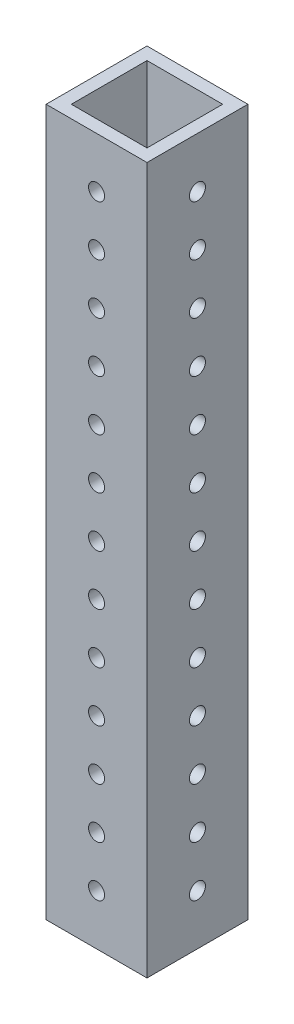
SolidWorks part; units mm, degrees
material "6061 Alloy"
ref_plane "Front Plane" through (0, 0, 0) normal (0, 0, 1) x (1, 0, 0)
ref_plane "Top Plane" through (0, 0, 0) normal (0, 1, 0) x (1, 0, 0)
ref_plane "Right Plane" through (0, 0, 0) normal (1, 0, 0) x (0, 0, -1)
sketch "Sketch1" plane through (0, 0, 0) normal (0, 1, 0) x (1, 0, 0)
  line L0 (9.525, 9.525) -> (-9.525, 9.525)
  line L1 (12.7, -12.7) -> (-12.7, -12.7)
  line L2 (12.7, -12.7) -> (12.7, 12.7)
  line L3 (12.7, 12.7) -> (-12.7, 12.7)
  line L4 (-12.7, -12.7) -> (-12.7, 12.7)
  line L5 (12.7, -12.7) -> (-12.7, 12.7) construction
  line L6 (12.7, 12.7) -> (-12.7, -12.7) construction
  line L7 (-9.525, -9.525) -> (-9.525, 9.525)
  line L8 (9.525, -9.525) -> (-9.525, -9.525)
  line L9 (9.525, -9.525) -> (9.525, 9.525)
  point P0 (0, 0)
  dimension "D1" = 25.4
  dimension "D2" = 25.4
  dimension "D3" = 3.175
extrude "Boss-Extrude1" add sketch "Sketch1" along normal blind 177.8
hole_wizard "#21 (0.159) Diameter Hole1" positions "Sketch2" profile "Sketch3" hole size "#21" standard "ANSI Inch" end condition through all
sketch "Sketch2" plane through (-12.7, 0, 0) normal (-1, 0, 0) x (0, 0, 1)
  line L0 (-12.7, 0) -> (12.7, 0) construction
  line L1 (12.7, 177.8) -> (12.7, 0) construction
  point P0 (0, 12.7)
  dimension "D1" = 12.7
  dimension "D2" = 12.7
sketch "Sketch3" plane through (-12.7, 12.7, 0) normal (0, 1, 0) x (0, 0, 1)
  line L0 (0, 0) -> (0, 25.4)
  line L1 (0, 25.4) -> (2.0193, 25.4)
  line L2 (2.0193, 25.4) -> (2.0193, 0)
  line L5 (2.0193, 0) -> (0, 0)
  line L11 (0, -6.35) -> (0, 107.95) construction
  dimension "Thru Hole Dia." = 4.0386
  dimension "Thru Hole Depth" = 25.4
pattern_linear "LPattern1" count 13 spacing 12.7 along (0, 1, 0) of "#21 (0.159) Diameter Hole1"
hole_wizard "#21 (0.159) Diameter Hole2" positions "Sketch4" profile "Sketch5" hole size "#21" standard "ANSI Inch" end condition through all
sketch "Sketch4" plane through (0, 0, -12.7) normal (0, 0, -1) x (-1, 0, 0)
  line L0 (-12.7, 177.8) -> (-12.7, 0) construction
  line L1 (-12.7, 0) -> (12.7, 0) construction
  point P0 (0, 12.7)
  dimension "D1" = 12.7
  dimension "D2" = 12.7
sketch "Sketch5" plane through (0, 12.7, -12.7) normal (1, 0, 0) x (0, 1, 0)
  line L0 (0, 0) -> (0, 25.4)
  line L1 (0, 25.4) -> (2.0193, 25.4)
  line L2 (2.0193, 25.4) -> (2.0193, 0)
  line L5 (2.0193, 0) -> (0, 0)
  line L11 (0, -6.35) -> (0, 107.95) construction
  dimension "Thru Hole Dia." = 4.0386
  dimension "Thru Hole Depth" = 25.4
pattern_linear "LPattern2" count 13 spacing 12.7 along (0, 1, 0) of "#21 (0.159) Diameter Hole2"
